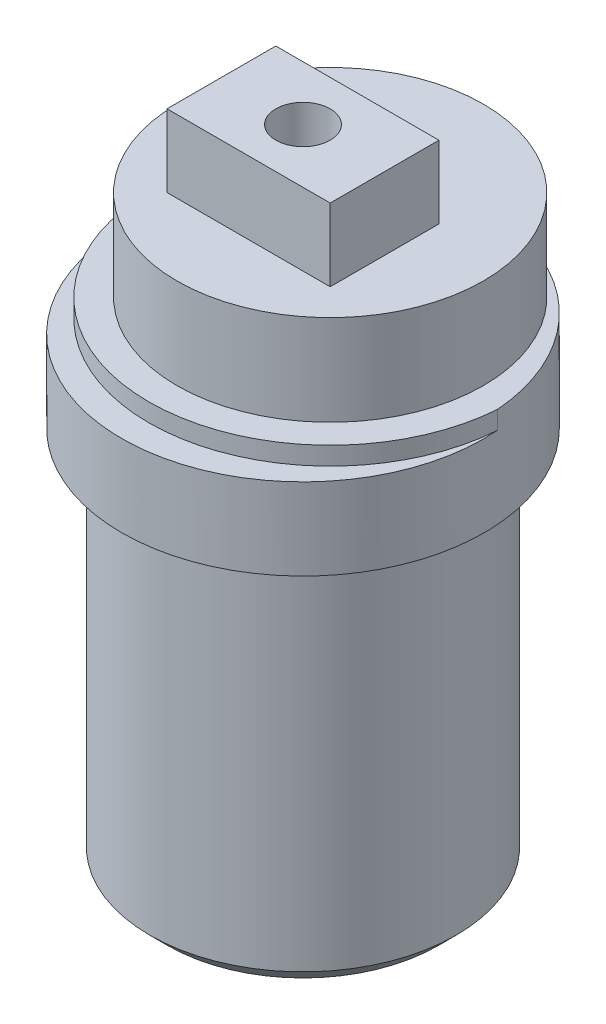
SolidWorks part; units mm, degrees
ref_plane "Front Plane" through (0, 0, 0) normal (0, 0, 1) x (1, 0, 0)
ref_plane "Top Plane" through (0, 0, 0) normal (0, 1, 0) x (1, 0, 0)
ref_plane "Right Plane" through (0, 0, 0) normal (1, 0, 0) x (0, 0, -1)
sketch "Sketch1" plane through (0, 0, 0) normal (0, 1, 0) x (1, 0, 0)
  circle A0 centre (0, 0) radius 8.45
  dimension "D1" = 16.9
extrude "Boss-Extrude1" add sketch "Sketch1" along normal blind 21
sketch "Sketch2" plane through (0, 21, 0) normal (0, 1, 0) x (1, 0, 0)
  circle A0 centre (0, 0) radius 10
  dimension "D1" = 20
extrude "Boss-Extrude2" add sketch "Sketch2" along normal blind 4.5
sketch "Sketch3" plane through (0, 25.5, 0) normal (0, 1, 0) x (1, 0, 0)
  circle A0 centre (0, 1.5) radius 8.45
  dimension "D1" = 16.9
  dimension "D2" = 1.5
extrude "Boss-Extrude3" add sketch "Sketch3" along normal blind 6
sketch "Sketch4" plane through (0, 25.5, 0) normal (0, 1, 0) x (1, 0, 0)
  circle A0 centre (0, 1.5) radius 8.45 construction
  circle A1 centre (0, 1.5) radius 8.45
  circle A2 centre (0, 0) radius 10 construction
  arc A3 (0, -10) -> (-9.9718, 0.75) centre (0, 0) ccw
  arc A4 (-9.9718, 0.75) -> (9.9718, 0.75) centre (0, 1.5) ccw
  arc A5 (9.9718, 0.75) -> (0, -10) centre (0, 0) ccw
  circle M1 centre (0, 1.5) radius 8.45
  circle M2 centre (0, 0) radius 10
  dimension "D1" = 20
extrude "Boss-Extrude4" add sketch "Sketch4" along normal blind 1 contours A4 M2 M1
sketch "Sketch5" plane through (0, 31.5, 0) normal (0, 1, 0) x (1, 0, 0)
  line L1 (-4.5, -3) -> (4.5, -3)
  line L2 (-4.5, -3) -> (-4.5, 3)
  line L3 (-4.5, 3) -> (4.5, 3)
  line L4 (4.5, -3) -> (4.5, 3)
  line L5 (-4.5, -3) -> (4.5, 3) construction
  line L6 (-4.5, 3) -> (4.5, -3) construction
  point P2 (0, 0)
  dimension "D3" = 9
  dimension "D4" = 6
extrude "Boss-Extrude5" add sketch "Sketch5" along normal blind 4
sketch "Sketch6" plane through (0, 35.5, 0) normal (0, 1, 0) x (1, 0, 0)
  circle A0 centre (0, 0) radius 1.5
  dimension "D1" = 3
extrude "Cut-Extrude1" cut sketch "Sketch6" against normal blind 8
sketch "Sketch7" plane through (0, 0, 0) normal (0, -1, 0) x (-1, 0, 0)
  circle A0 centre (0, -5.5) radius 1.5
  circle A1 centre (-5.5, 0) radius 1.5
  circle A2 centre (0, 5.5) radius 1.5
  circle A3 centre (5.5, 0) radius 1.5
  point P12 (0, 0)
  dimension "D3" = 3
  dimension "D1" = 5.5
  dimension "D2" = 4
extrude "Cut-Extrude2" [suppressed] cut sketch "Sketch7" against normal blind 8
sketch "Sketch8" plane through (0, 0, 0) normal (0, -1, 0) x (1, 0, 0)
  arc A0 (1.9433, 2.9259) -> (1.4435, 3.2021) centre (0, 0) ccw
  arc A1 (-2.4201, 2.5457) -> (-2.8006, 2.1199) centre (0, 0) ccw
  arc A2 (3.4992, 0.3049) -> (3.4036, 0.8679) centre (0, 0) ccw
  arc A3 (2.4201, -2.5457) -> (2.8006, -2.1199) centre (0, 0) ccw
  arc A4 (-1.0759, 3.3436) -> (-1.6035, 3.1251) centre (0, 0) ccw
  arc A5 (-3.0204, -1.793) -> (-2.6899, -2.2587) centre (0, 0) ccw
  arc A6 (0.4814, 3.4793) -> (-0.0888, 3.5113) centre (0, 0) ccw
  arc A7 (3.0204, 1.793) -> (2.6899, 2.2587) centre (0, 0) ccw
  arc A8 (3.285, -1.2435) -> (3.4431, -0.6948) centre (0, 0) ccw
  arc A9 (-3.285, 1.2435) -> (-3.4431, 0.6948) centre (0, 0) ccw
  arc A10 (1.0759, -3.3436) -> (1.6035, -3.1251) centre (0, 0) ccw
  arc A11 (-1.9433, -2.9259) -> (-1.4435, -3.2021) centre (0, 0) ccw
  arc A12 (-0.4814, -3.4793) -> (0.0888, -3.5113) centre (0, 0) ccw
  arc A13 (-3.4992, -0.3049) -> (-3.4036, -0.8679) centre (0, 0) ccw
  spline S0 degree 3 poles (-2.6899, -2.2587) (-2.6998, -2.278) (-2.7192, -2.3185) (-2.7467, -2.3829) (-2.7734, -2.4537) (-2.7988, -2.5314) (-2.8225, -2.6162) (-2.8438, -2.7079) (-2.8627, -2.8065) (-2.877, -2.9191) (-2.8909, -3.0073) (-2.8865, -3.0684) (-2.8815, -3.0926) (-2.874, -3.1162) (-2.8635, -3.1386) (-2.8488, -3.1646) (-2.8257, -3.1852) (-2.7982, -3.1969) (-2.7748, -3.2048) (-2.7506, -3.2097) (-2.7259, -3.2119) (-2.6647, -3.2094) (-2.5786, -3.1858) (-2.4684, -3.1589) (-2.3725, -3.1291) (-2.2837, -3.0977) (-2.2021, -3.0646) (-2.1277, -3.0307) (-2.0604, -2.9963) (-1.9994, -2.9617) (-1.9614, -2.9379) (-1.9433, -2.9259) knots 0.027203 0.027203 0.027203 0.027203 0.059318 0.093556 0.130845 0.171187 0.214581 0.261026 0.310525 0.363075 0.429245 0.441417 0.453589 0.465761 0.477933 0.490104 0.509896 0.522067 0.534239 0.546411 0.558583 0.570755 0.636925 0.689475 0.738974 0.785419 0.828813 0.869155 0.906444 0.940682 0.972797 0.972797 0.972797 0.972797 weights 1 1 1 1 1 1 1 1 1 1 1 1 1 1 1 1 1 1 1 1 1 1 1 1 1 1 1 1 1 1 1 1
  spline S1 degree 3 poles (-1.6035, 3.1251) (-1.6202, 3.139) (-1.6552, 3.1669) (-1.7119, 3.2081) (-1.775, 3.2498) (-1.8451, 3.2919) (-1.9225, 3.3339) (-2.0072, 3.3751) (-2.0992, 3.4154) (-2.2057, 3.4545) (-2.2886, 3.4876) (-2.3492, 3.4969) (-2.3739, 3.4975) (-2.3985, 3.4953) (-2.4227, 3.4901) (-2.4514, 3.4815) (-2.4765, 3.4637) (-2.4941, 3.4395) (-2.507, 3.4184) (-2.5172, 3.3958) (-2.5248, 3.3723) (-2.536, 3.312) (-2.5321, 3.2229) (-2.5304, 3.1094) (-2.5227, 3.0093) (-2.5119, 2.9157) (-2.4978, 2.8289) (-2.4812, 2.7487) (-2.4627, 2.6754) (-2.4425, 2.6083) (-2.4278, 2.566) (-2.4201, 2.5457) knots 0.027203 0.027203 0.027203 0.027203 0.059318 0.093556 0.130845 0.171187 0.214581 0.261026 0.310525 0.363075 0.429245 0.441417 0.453589 0.465761 0.477933 0.490104 0.509896 0.522067 0.534239 0.546411 0.558583 0.570755 0.636925 0.689475 0.738974 0.785419 0.828813 0.869155 0.906444 0.940682 0.972797 0.972797 0.972797 0.972797 weights 1 1 1 1 1 1 1 1 1 1 1 1 1 1 1 1 1 1 1 1 1 1 1 1 1 1 1 1 1 1 1 1
  spline S2 degree 3 poles (2.6899, 2.2587) (2.6998, 2.278) (2.7192, 2.3185) (2.7467, 2.3829) (2.7734, 2.4537) (2.7988, 2.5314) (2.8225, 2.6162) (2.8438, 2.7079) (2.8627, 2.8065) (2.877, 2.9191) (2.8909, 3.0073) (2.8865, 3.0684) (2.8815, 3.0926) (2.874, 3.1162) (2.8635, 3.1386) (2.8488, 3.1646) (2.8257, 3.1852) (2.7982, 3.1969) (2.7748, 3.2048) (2.7506, 3.2097) (2.7259, 3.2119) (2.6647, 3.2094) (2.5786, 3.1858) (2.4684, 3.1589) (2.3725, 3.1291) (2.2837, 3.0977) (2.2021, 3.0646) (2.1277, 3.0307) (2.0604, 2.9963) (1.9994, 2.9617) (1.9614, 2.9379) (1.9433, 2.9259) knots 0.027203 0.027203 0.027203 0.027203 0.059318 0.093556 0.130845 0.171187 0.214581 0.261026 0.310525 0.363075 0.429245 0.441417 0.453589 0.465761 0.477933 0.490104 0.509896 0.522067 0.534239 0.546411 0.558583 0.570755 0.636925 0.689475 0.738974 0.785419 0.828813 0.869155 0.906444 0.940682 0.972797 0.972797 0.972797 0.972797 weights 1 1 1 1 1 1 1 1 1 1 1 1 1 1 1 1 1 1 1 1 1 1 1 1 1 1 1 1 1 1 1 1
  spline S3 degree 3 poles (3.4036, 0.8679) (3.4208, 0.881) (3.4559, 0.909) (3.5086, 0.9551) (3.5633, 1.0074) (3.62, 1.0664) (3.6781, 1.1324) (3.7371, 1.2058) (3.7969, 1.2865) (3.8587, 1.3817) (3.9094, 1.4551) (3.9319, 1.5121) (3.938, 1.5361) (3.9414, 1.5606) (3.9417, 1.5853) (3.9397, 1.6152) (3.9279, 1.6437) (3.9082, 1.6662) (3.8905, 1.6835) (3.8708, 1.6984) (3.8495, 1.7111) (3.7933, 1.7354) (3.7055, 1.7515) (3.5945, 1.7751) (3.4952, 1.7899) (3.4016, 1.8001) (3.3137, 1.8057) (3.232, 1.8073) (3.1564, 1.8056) (3.0865, 1.8009) (3.0419, 1.7959) (3.0204, 1.793) knots 0.027203 0.027203 0.027203 0.027203 0.059318 0.093556 0.130845 0.171187 0.214581 0.261026 0.310525 0.363075 0.429245 0.441417 0.453589 0.465761 0.477933 0.490104 0.509896 0.522067 0.534239 0.546411 0.558583 0.570755 0.636925 0.689475 0.738974 0.785419 0.828813 0.869155 0.906444 0.940682 0.972797 0.972797 0.972797 0.972797 weights 1 1 1 1 1 1 1 1 1 1 1 1 1 1 1 1 1 1 1 1 1 1 1 1 1 1 1 1 1 1 1 1
  spline S4 degree 3 poles (2.8006, -2.1199) (2.8217, -2.1252) (2.8654, -2.1351) (2.9343, -2.1476) (3.0093, -2.1578) (3.0907, -2.1653) (3.1786, -2.1696) (3.2728, -2.1699) (3.3732, -2.1664) (3.4861, -2.1553) (3.5751, -2.1492) (3.6338, -2.1313) (3.6563, -2.1211) (3.6776, -2.1085) (3.6971, -2.0933) (3.7192, -2.0731) (3.7341, -2.0461) (3.7394, -2.0167) (3.7419, -1.9921) (3.7413, -1.9674) (3.7379, -1.9429) (3.7219, -1.8837) (3.6797, -1.8051) (3.629, -1.7036) (3.5786, -1.6167) (3.5282, -1.5371) (3.4778, -1.465) (3.4281, -1.4) (3.3796, -1.342) (3.3324, -1.2903) (3.3007, -1.2585) (3.285, -1.2435) knots 0.027203 0.027203 0.027203 0.027203 0.059318 0.093556 0.130845 0.171187 0.214581 0.261026 0.310525 0.363075 0.429245 0.441417 0.453589 0.465761 0.477933 0.490104 0.509896 0.522067 0.534239 0.546411 0.558583 0.570755 0.636925 0.689475 0.738974 0.785419 0.828813 0.869155 0.906444 0.940682 0.972797 0.972797 0.972797 0.972797 weights 1 1 1 1 1 1 1 1 1 1 1 1 1 1 1 1 1 1 1 1 1 1 1 1 1 1 1 1 1 1 1 1
  spline S5 degree 3 poles (-2.8006, 2.1199) (-2.8217, 2.1252) (-2.8654, 2.1351) (-2.9343, 2.1476) (-3.0093, 2.1578) (-3.0907, 2.1653) (-3.1786, 2.1696) (-3.2728, 2.1699) (-3.3732, 2.1664) (-3.4861, 2.1553) (-3.5751, 2.1492) (-3.6338, 2.1313) (-3.6563, 2.1211) (-3.6776, 2.1085) (-3.6971, 2.0933) (-3.7192, 2.0731) (-3.7341, 2.0461) (-3.7394, 2.0167) (-3.7419, 1.9921) (-3.7413, 1.9674) (-3.7379, 1.9429) (-3.7219, 1.8837) (-3.6797, 1.8051) (-3.629, 1.7036) (-3.5786, 1.6167) (-3.5282, 1.5371) (-3.4778, 1.465) (-3.4281, 1.4) (-3.3796, 1.342) (-3.3324, 1.2903) (-3.3007, 1.2585) (-3.285, 1.2435) knots 0.027203 0.027203 0.027203 0.027203 0.059318 0.093556 0.130845 0.171187 0.214581 0.261026 0.310525 0.363075 0.429245 0.441417 0.453589 0.465761 0.477933 0.490104 0.509896 0.522067 0.534239 0.546411 0.558583 0.570755 0.636925 0.689475 0.738974 0.785419 0.828813 0.869155 0.906444 0.940682 0.972797 0.972797 0.972797 0.972797 weights 1 1 1 1 1 1 1 1 1 1 1 1 1 1 1 1 1 1 1 1 1 1 1 1 1 1 1 1 1 1 1 1
  spline S6 degree 3 poles (1.4435, 3.2021) (1.444, 3.2238) (1.444, 3.2687) (1.4408, 3.3387) (1.4341, 3.414) (1.4233, 3.4951) (1.4079, 3.5817) (1.3873, 3.6736) (1.3615, 3.7707) (1.3256, 3.8783) (1.2998, 3.9638) (1.2693, 4.0169) (1.2543, 4.0366) (1.2373, 4.0546) (1.2182, 4.0702) (1.1936, 4.0872) (1.1639, 4.0958) (1.134, 4.0944) (1.1095, 4.0914) (1.0855, 4.0852) (1.0624, 4.0765) (1.0083, 4.0478) (0.941, 3.9891) (0.8533, 3.9171) (0.7798, 3.8486) (0.7135, 3.7818) (0.6543, 3.7166) (0.6021, 3.6537) (0.5563, 3.5935) (0.5164, 3.5359) (0.4925, 3.498) (0.4814, 3.4793) knots 0.027203 0.027203 0.027203 0.027203 0.059318 0.093556 0.130845 0.171187 0.214581 0.261026 0.310525 0.363075 0.429245 0.441417 0.453589 0.465761 0.477933 0.490104 0.509896 0.522067 0.534239 0.546411 0.558583 0.570755 0.636925 0.689475 0.738974 0.785419 0.828813 0.869155 0.906444 0.940682 0.972797 0.972797 0.972797 0.972797 weights 1 1 1 1 1 1 1 1 1 1 1 1 1 1 1 1 1 1 1 1 1 1 1 1 1 1 1 1 1 1 1 1
  spline S7 degree 3 poles (-1.4435, -3.2021) (-1.444, -3.2238) (-1.444, -3.2687) (-1.4408, -3.3387) (-1.4341, -3.414) (-1.4233, -3.4951) (-1.4079, -3.5817) (-1.3873, -3.6736) (-1.3615, -3.7707) (-1.3256, -3.8783) (-1.2998, -3.9638) (-1.2693, -4.0169) (-1.2543, -4.0366) (-1.2373, -4.0546) (-1.2182, -4.0702) (-1.1936, -4.0872) (-1.1639, -4.0958) (-1.134, -4.0944) (-1.1095, -4.0914) (-1.0855, -4.0852) (-1.0624, -4.0765) (-1.0083, -4.0478) (-0.941, -3.9891) (-0.8533, -3.9171) (-0.7798, -3.8486) (-0.7135, -3.7818) (-0.6543, -3.7166) (-0.6021, -3.6537) (-0.5563, -3.5935) (-0.5164, -3.5359) (-0.4925, -3.498) (-0.4814, -3.4793) knots 0.027203 0.027203 0.027203 0.027203 0.059318 0.093556 0.130845 0.171187 0.214581 0.261026 0.310525 0.363075 0.429245 0.441417 0.453589 0.465761 0.477933 0.490104 0.509896 0.522067 0.534239 0.546411 0.558583 0.570755 0.636925 0.689475 0.738974 0.785419 0.828813 0.869155 0.906444 0.940682 0.972797 0.972797 0.972797 0.972797 weights 1 1 1 1 1 1 1 1 1 1 1 1 1 1 1 1 1 1 1 1 1 1 1 1 1 1 1 1 1 1 1 1
  spline S8 degree 3 poles (-3.4036, -0.8679) (-3.4208, -0.881) (-3.4559, -0.909) (-3.5086, -0.9551) (-3.5633, -1.0074) (-3.62, -1.0664) (-3.6781, -1.1324) (-3.7371, -1.2058) (-3.7969, -1.2865) (-3.8587, -1.3817) (-3.9094, -1.4551) (-3.9319, -1.5121) (-3.938, -1.5361) (-3.9414, -1.5606) (-3.9417, -1.5853) (-3.9397, -1.6152) (-3.9279, -1.6437) (-3.9082, -1.6662) (-3.8905, -1.6835) (-3.8708, -1.6984) (-3.8495, -1.7111) (-3.7933, -1.7354) (-3.7055, -1.7515) (-3.5945, -1.7751) (-3.4952, -1.7899) (-3.4016, -1.8001) (-3.3137, -1.8057) (-3.232, -1.8073) (-3.1564, -1.8056) (-3.0865, -1.8009) (-3.0419, -1.7959) (-3.0204, -1.793) knots 0.027203 0.027203 0.027203 0.027203 0.059318 0.093556 0.130845 0.171187 0.214581 0.261026 0.310525 0.363075 0.429245 0.441417 0.453589 0.465761 0.477933 0.490104 0.509896 0.522067 0.534239 0.546411 0.558583 0.570755 0.636925 0.689475 0.738974 0.785419 0.828813 0.869155 0.906444 0.940682 0.972797 0.972797 0.972797 0.972797 weights 1 1 1 1 1 1 1 1 1 1 1 1 1 1 1 1 1 1 1 1 1 1 1 1 1 1 1 1 1 1 1 1
  spline S9 degree 3 poles (3.4431, -0.6948) (3.4643, -0.6905) (3.508, -0.6804) (3.5756, -0.6618) (3.6475, -0.6385) (3.7242, -0.6099) (3.8052, -0.5756) (3.8902, -0.535) (3.9791, -0.4883) (4.0761, -0.4293) (4.1536, -0.3852) (4.1987, -0.3436) (4.2145, -0.3246) (4.2282, -0.304) (4.2392, -0.2819) (4.2504, -0.2541) (4.2521, -0.2233) (4.2441, -0.1945) (4.2357, -0.1713) (4.2244, -0.1493) (4.2107, -0.1286) (4.1706, -0.0823) (4.0985, -0.0298) (4.0087, 0.0397) (3.9256, 0.0961) (3.8457, 0.1459) (3.769, 0.1891) (3.6961, 0.2261) (3.6272, 0.2573) (3.5622, 0.2834) (3.5199, 0.2982) (3.4992, 0.3049) knots 0.027203 0.027203 0.027203 0.027203 0.059318 0.093556 0.130845 0.171187 0.214581 0.261026 0.310525 0.363075 0.429245 0.441417 0.453589 0.465761 0.477933 0.490104 0.509896 0.522067 0.534239 0.546411 0.558583 0.570755 0.636925 0.689475 0.738974 0.785419 0.828813 0.869155 0.906444 0.940682 0.972797 0.972797 0.972797 0.972797 weights 1 1 1 1 1 1 1 1 1 1 1 1 1 1 1 1 1 1 1 1 1 1 1 1 1 1 1 1 1 1 1 1
  spline S10 degree 3 poles (-0.0888, 3.5113) (-0.0977, 3.5311) (-0.1172, 3.5715) (-0.1505, 3.6332) (-0.1892, 3.6981) (-0.2341, 3.7665) (-0.2856, 3.8379) (-0.344, 3.9117) (-0.4094, 3.988) (-0.4885, 4.0694) (-0.5487, 4.1352) (-0.5993, 4.1698) (-0.6213, 4.1811) (-0.6444, 4.1899) (-0.6685, 4.1957) (-0.698, 4.2003) (-0.7284, 4.1952) (-0.7548, 4.181) (-0.7755, 4.1676) (-0.7945, 4.1517) (-0.8116, 4.1338) (-0.8478, 4.0844) (-0.883, 4.0024) (-0.9307, 3.8994) (-0.9672, 3.8058) (-0.998, 3.7168) (-1.023, 3.6325) (-1.0429, 3.5531) (-1.058, 3.479) (-1.0689, 3.4098) (-1.074, 3.3652) (-1.0759, 3.3436) knots 0.027203 0.027203 0.027203 0.027203 0.059318 0.093556 0.130845 0.171187 0.214581 0.261026 0.310525 0.363075 0.429245 0.441417 0.453589 0.465761 0.477933 0.490104 0.509896 0.522067 0.534239 0.546411 0.558583 0.570755 0.636925 0.689475 0.738974 0.785419 0.828813 0.869155 0.906444 0.940682 0.972797 0.972797 0.972797 0.972797 weights 1 1 1 1 1 1 1 1 1 1 1 1 1 1 1 1 1 1 1 1 1 1 1 1 1 1 1 1 1 1 1 1
  spline S11 degree 3 poles (1.6035, -3.1251) (1.6202, -3.139) (1.6552, -3.1669) (1.7119, -3.2081) (1.775, -3.2498) (1.8451, -3.2919) (1.9225, -3.3339) (2.0072, -3.3751) (2.0992, -3.4154) (2.2057, -3.4545) (2.2886, -3.4876) (2.3492, -3.4969) (2.3739, -3.4975) (2.3985, -3.4953) (2.4227, -3.4901) (2.4514, -3.4815) (2.4765, -3.4637) (2.4941, -3.4395) (2.507, -3.4184) (2.5172, -3.3958) (2.5248, -3.3723) (2.536, -3.312) (2.5321, -3.2229) (2.5304, -3.1094) (2.5227, -3.0093) (2.5119, -2.9157) (2.4978, -2.8289) (2.4812, -2.7487) (2.4627, -2.6754) (2.4425, -2.6083) (2.4278, -2.566) (2.4201, -2.5457) knots 0.027203 0.027203 0.027203 0.027203 0.059318 0.093556 0.130845 0.171187 0.214581 0.261026 0.310525 0.363075 0.429245 0.441417 0.453589 0.465761 0.477933 0.490104 0.509896 0.522067 0.534239 0.546411 0.558583 0.570755 0.636925 0.689475 0.738974 0.785419 0.828813 0.869155 0.906444 0.940682 0.972797 0.972797 0.972797 0.972797 weights 1 1 1 1 1 1 1 1 1 1 1 1 1 1 1 1 1 1 1 1 1 1 1 1 1 1 1 1 1 1 1 1
  spline S12 degree 3 poles (-3.4431, 0.6948) (-3.4643, 0.6905) (-3.508, 0.6804) (-3.5756, 0.6618) (-3.6475, 0.6385) (-3.7242, 0.6099) (-3.8052, 0.5756) (-3.8902, 0.535) (-3.9791, 0.4883) (-4.0761, 0.4293) (-4.1536, 0.3852) (-4.1987, 0.3436) (-4.2145, 0.3246) (-4.2282, 0.304) (-4.2392, 0.2819) (-4.2504, 0.2541) (-4.2521, 0.2233) (-4.2441, 0.1945) (-4.2357, 0.1713) (-4.2244, 0.1493) (-4.2107, 0.1286) (-4.1706, 0.0823) (-4.0985, 0.0298) (-4.0087, -0.0397) (-3.9256, -0.0961) (-3.8457, -0.1459) (-3.769, -0.1891) (-3.6961, -0.2261) (-3.6272, -0.2573) (-3.5622, -0.2834) (-3.5199, -0.2982) (-3.4992, -0.3049) knots 0.027203 0.027203 0.027203 0.027203 0.059318 0.093556 0.130845 0.171187 0.214581 0.261026 0.310525 0.363075 0.429245 0.441417 0.453589 0.465761 0.477933 0.490104 0.509896 0.522067 0.534239 0.546411 0.558583 0.570755 0.636925 0.689475 0.738974 0.785419 0.828813 0.869155 0.906444 0.940682 0.972797 0.972797 0.972797 0.972797 weights 1 1 1 1 1 1 1 1 1 1 1 1 1 1 1 1 1 1 1 1 1 1 1 1 1 1 1 1 1 1 1 1
  spline S13 degree 3 poles (0.0888, -3.5113) (0.0977, -3.5311) (0.1172, -3.5715) (0.1505, -3.6332) (0.1892, -3.6981) (0.2341, -3.7665) (0.2856, -3.8379) (0.344, -3.9117) (0.4094, -3.988) (0.4885, -4.0694) (0.5487, -4.1352) (0.5993, -4.1698) (0.6213, -4.1811) (0.6444, -4.1899) (0.6685, -4.1957) (0.698, -4.2003) (0.7284, -4.1952) (0.7548, -4.181) (0.7755, -4.1676) (0.7945, -4.1517) (0.8116, -4.1338) (0.8478, -4.0844) (0.883, -4.0024) (0.9307, -3.8994) (0.9672, -3.8058) (0.998, -3.7168) (1.023, -3.6325) (1.0429, -3.5531) (1.058, -3.479) (1.0689, -3.4098) (1.074, -3.3652) (1.0759, -3.3436) knots 0.027203 0.027203 0.027203 0.027203 0.059318 0.093556 0.130845 0.171187 0.214581 0.261026 0.310525 0.363075 0.429245 0.441417 0.453589 0.465761 0.477933 0.490104 0.509896 0.522067 0.534239 0.546411 0.558583 0.570755 0.636925 0.689475 0.738974 0.785419 0.828813 0.869155 0.906444 0.940682 0.972797 0.972797 0.972797 0.972797 weights 1 1 1 1 1 1 1 1 1 1 1 1 1 1 1 1 1 1 1 1 1 1 1 1 1 1 1 1 1 1 1 1
extrude "Cut-Extrude3" cut sketch "Sketch8" against normal blind 30
chamfer "Chamfer1" distance 1 angle 45 1 edges at (0, 0, 8.45)
